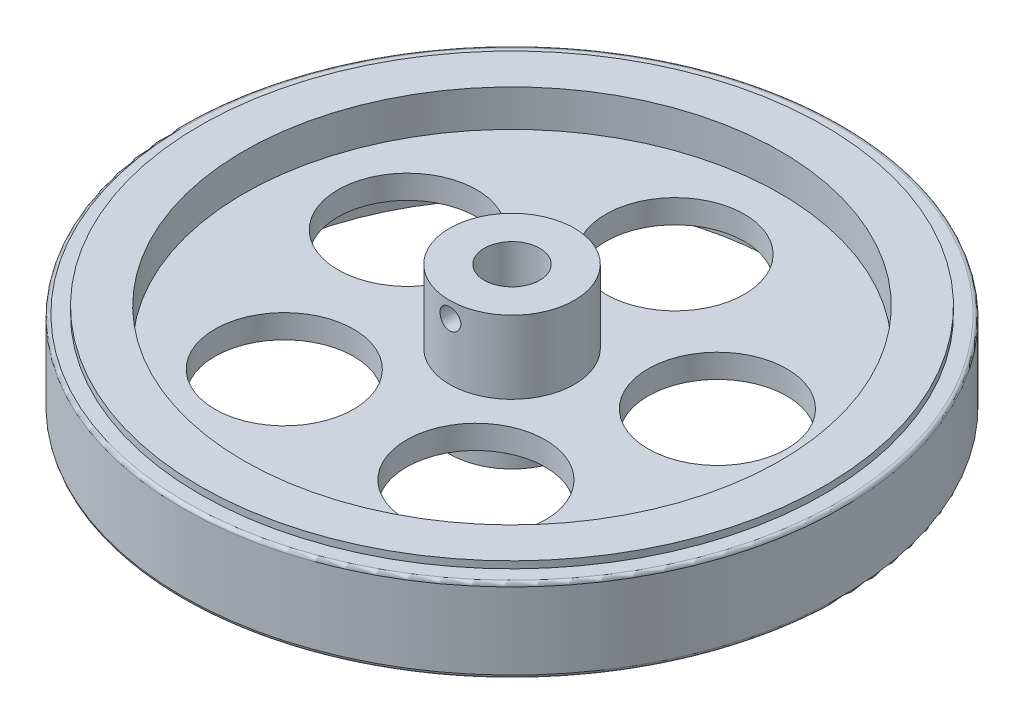
SolidWorks part; units mm, degrees
ref_plane "前基準面" through (0, 0, 0) normal (0, 0, 1) x (1, 0, 0)
ref_plane "上基準面" through (0, 0, 0) normal (0, 1, 0) x (1, 0, 0)
ref_plane "右基準面" through (0, 0, 0) normal (1, 0, 0) x (0, 0, -1)
sketch "草圖1" plane through (0, 0, 0) normal (0, 1, 0) x (1, 0, 0)
  circle A0 centre (0, 0) radius 47.5
  circle A1 centre (0, 0) radius 9
  circle A2 centre (0, 0) radius 4
  dimension "D1" = 95
  dimension "D2" = 18
  dimension "D3" = 8
extrude "填料-伸長1" add sketch "草圖1" along normal mid plane 14 contours A0 A1 | A1 A2
sketch "草圖2" plane through (0, 7, 0) normal (0, 1, 0) x (1, 0, 0)
  circle A0 centre (0, 0) radius 47.5
  circle A1 centre (0, 0) radius 45
  dimension "D1" = 90
extrude "除料-伸長1" cut sketch "草圖2" against normal blind 1
mirror "鏡射1" about plane through (0, 0, 0) normal (0, 1, 0) of "除料-伸長1"
sketch "草圖3" plane through (0, 7, 0) normal (0, 1, 0) x (1, 0, 0)
  circle A0 centre (0, 0) radius 38.66
  circle A1 centre (0, 0) radius 9
  dimension "D1" = 77.32
  dimension "D2" = 18
extrude "除料-伸長2" cut sketch "草圖3" against normal blind 5.3
mirror "鏡射2" about plane through (0, 0, 0) normal (0, 1, 0) of "除料-伸長2"
sketch "草圖4" plane through (0, 1.7, 0) normal (0, 1, 0) x (1, 0, 0)
  line L0 (0, 0) -> (0, 42.0413) construction
  circle A0 centre (0, 23.5) radius 10
  circle A1 centre (0, 0) radius 4 construction
  circle A2 centre (22.3498, 7.2619) radius 10
  circle A3 centre (13.813, -19.0119) radius 10
  circle A4 centre (-13.813, -19.0119) radius 10
  circle A5 centre (-22.3498, 7.2619) radius 10
  point P17 (0, 0)
  dimension "D1" = 20
  dimension "D2" = 23.5
  dimension "D3" = 5
extrude "除料-伸長3" cut sketch "草圖4" against normal through all
fillet "圓角1" radius 0.5 2 edges at (0, -6, 47.5) (0, 6, 47.5)
sketch "草圖5" plane through (0, 7, 0) normal (0, 1, 0) x (1, 0, 0)
  circle A0 centre (0, 0) radius 9
  circle A1 centre (0, 0) radius 4
extrude "填料-伸長2" add sketch "草圖5" along normal blind 5.2
sketch "草圖6" plane through (0, 0, 0) normal (0, 0, 1) x (1, 0, 0)
  line L0 (0, 13.3385) -> (0, 0) construction
  line L1 (9, 12.2) -> (-9, 12.2) construction
  circle A0 centre (0, 9.9) radius 1.5
  dimension "D2" = 3
  dimension "D1" = 2.3
extrude "除料-伸長4" cut sketch "草圖6" along normal through all
